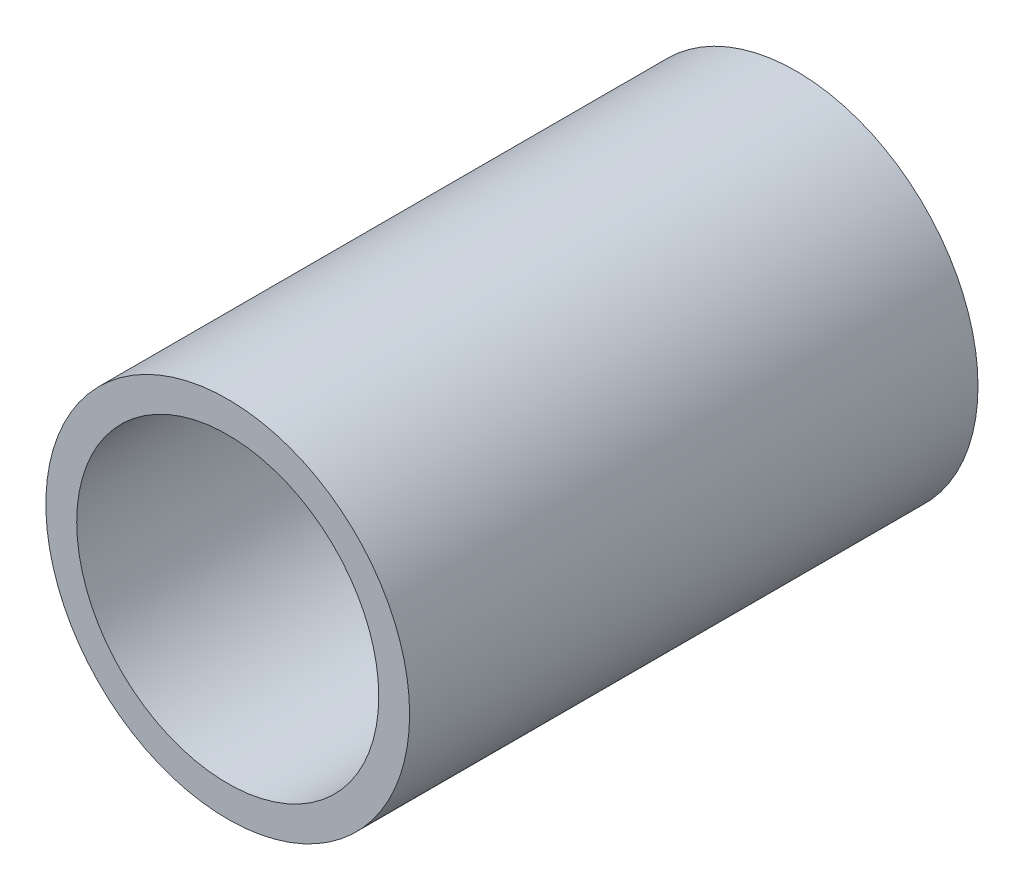
SolidWorks part; units mm, degrees
ref_plane "Front Plane" through (0, 0, 0) normal (0, 0, 1) x (1, 0, 0)
ref_plane "Top Plane" through (0, 0, 0) normal (0, 1, 0) x (1, 0, 0)
ref_plane "Right Plane" through (0, 0, 0) normal (1, 0, 0) x (0, 0, -1)
sketch "Sketch1" plane through (0, 0, 0) normal (0, 0, 1) x (1, 0, 0)
  circle A0 centre (0, 0) radius 16
  circle A1 centre (0, 0) radius 13.2855
extrude "Boss-Extrude1" add sketch "Sketch1" along normal blind 50
